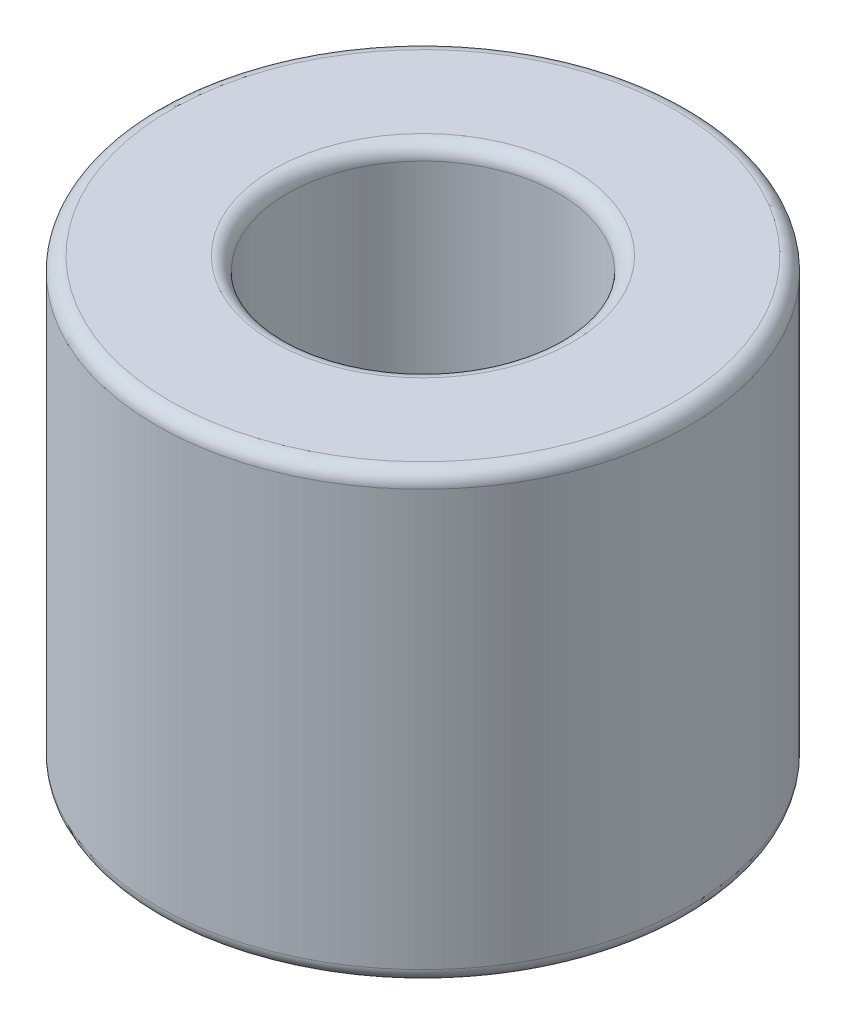
SolidWorks part; units mm, degrees
material "6061-T6 (SS)"
ref_plane "Plan de face" through (0, 0, 0) normal (0, 0, 1) x (1, 0, 0)
ref_plane "Plan de dessus" through (0, 0, 0) normal (0, 1, 0) x (1, 0, 0)
ref_plane "Plan de droite" through (0, 0, 0) normal (1, 0, 0) x (0, 0, -1)
sketch "Esquisse2" plane through (0, 0, 0) normal (0, 1, 0) x (1, 0, 0)
  circle A0 centre (0, 0) radius 9.525
  circle A1 centre (0, 0) radius 4.8514
  dimension "D1" = 19.05
  dimension "D2" = 9.7028
extrude "Boss.-Extru.1" add sketch "Esquisse2" along normal mid plane 15.875
fillet "Congé2" radius 0.5 4 edges at (0, -7.9375, 4.8514) (0, -7.9375, 9.525) (0, 7.9375, 4.8514) (0, 7.9375, 9.525)
equation "\"LENGHT\"= 0.625po"
equation "\"D1@Boss.-Extru.1\"=\"LENGHT\""
equation "\"OD\"= 0.75po"
equation "\"D1@Esquisse2\"=\"OD\""
equation "\"ID\"= 0.382po"
equation "\"D2@Esquisse2\"=\"ID\""
